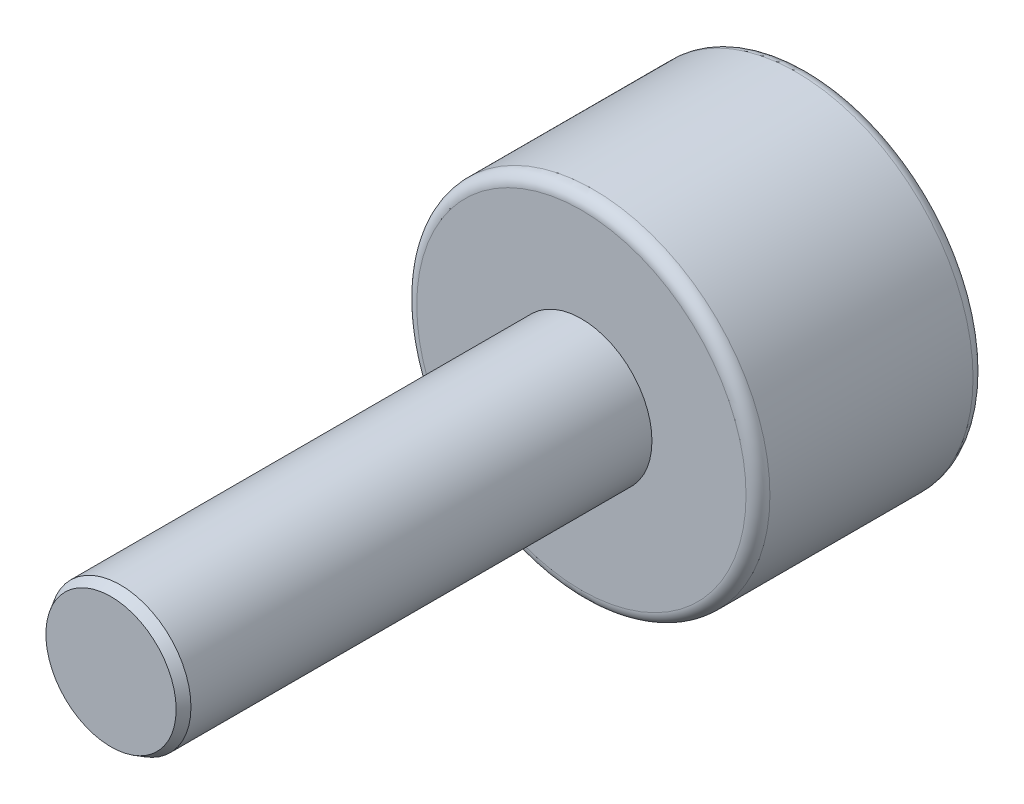
SolidWorks part; units mm, degrees
ref_plane "Front Plane" through (0, 0, 0) normal (0, 0, 1) x (1, 0, 0)
ref_plane "Top Plane" through (0, 0, 0) normal (0, 1, 0) x (1, 0, 0)
ref_plane "Right Plane" through (0, 0, 0) normal (1, 0, 0) x (0, 0, -1)
sketch "Sketch1" plane through (0, 0, 0) normal (0, 1, 0) x (1, 0, 0)
  line L0 (0, 0) -> (3.5, 0)
  line L1 (3.754, -0.254) -> (3.754, -4.572)
  line L2 (3.5, -4.826) -> (0, -4.826)
  line L3 (0, 0) -> (0, 1.0712) construction
  line L4 (0, 0) -> (0, -4.826)
  line L5 (0, 0) -> (0.1848, 0.1731) construction
  arc A0 (3.754, -4.572) -> (3.5, -4.826) centre (3.5, -4.572) cw
  arc A1 (3.754, -0.254) -> (3.5, 0) centre (3.5, -0.254) ccw
  point P6 (3.754, -4.826)
  point P9 (3.754, 0)
  dimension "D1" = 4.826
  dimension "D2" = 3.5
revolve "Revolve1" add sketch "Sketch1" angle 360 about L3
sketch "Sketch2" plane through (0, 0, 0) normal (0, 0, -1) x (-1, 0, 0)
  line L1 (0, 2.55) -> (-2.2084, 1.275)
  line L2 (-2.2084, 1.275) -> (-2.2084, -1.275)
  line L3 (-2.2084, -1.275) -> (0, -2.55)
  line L4 (0, -2.55) -> (2.2084, -1.275)
  line L5 (2.2084, -1.275) -> (2.2084, 1.275)
  line L6 (2.2084, 1.275) -> (0, 2.55)
  circle A0 centre (0, 0) radius 2.2084 construction
  dimension "D1" = 2.55
  dimension "D2" = 0
extrude "Cut-Extrude1" cut sketch "Sketch2" against normal blind 2.54
sketch "Sketch3" plane through (0, 0, 4.826) normal (0, 0, 1) x (1, 0, 0)
  circle A0 centre (0, 0) radius 1.5
  dimension "D1" = 3
extrude "Boss-Extrude1" add sketch "Sketch3" along normal blind 10
chamfer "Chamfer1" distance 0.2 angle 30 1 edges at (1.5, 0, 14.826)
